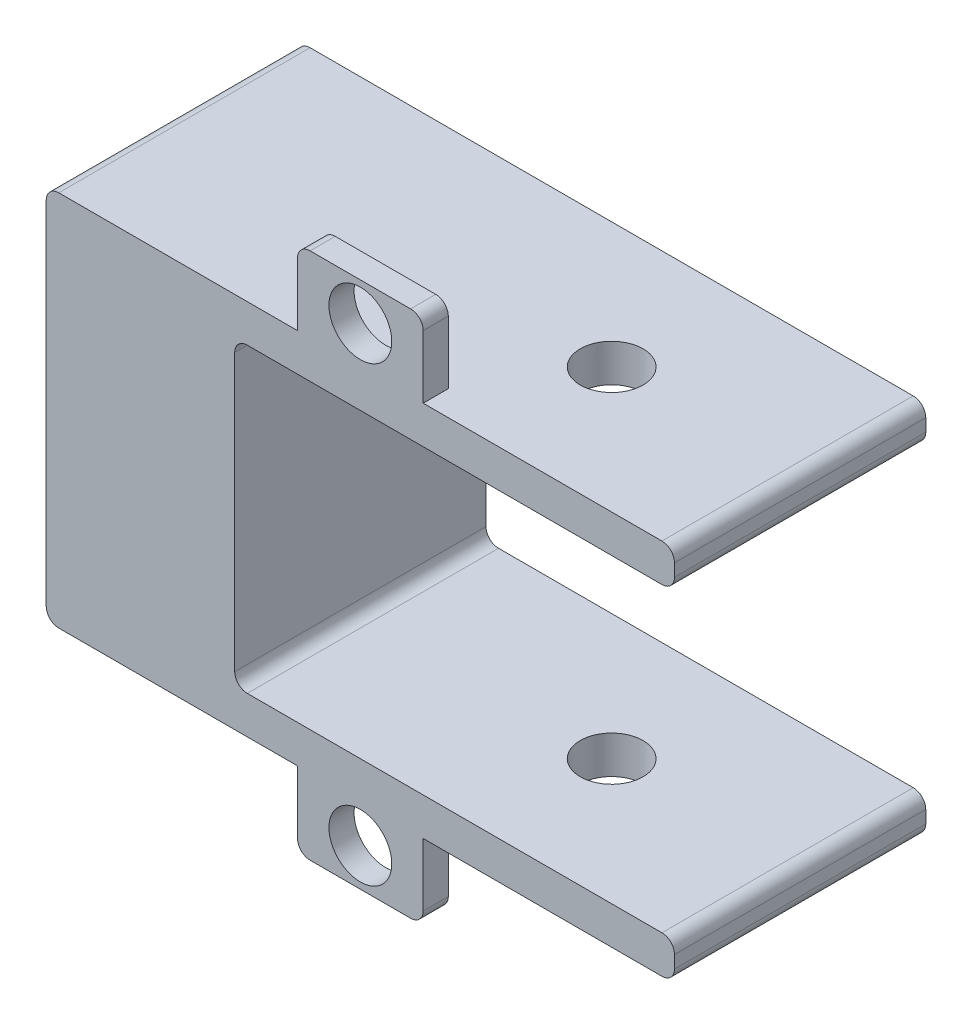
SolidWorks part; units mm, degrees
ref_plane "Front Plane" through (0, 0, 0) normal (0, 0, 1) x (1, 0, 0)
ref_plane "Top Plane" through (0, 0, 0) normal (0, 1, 0) x (1, 0, 0)
ref_plane "Right Plane" through (0, 0, 0) normal (1, 0, 0) x (0, 0, -1)
sketch "Sketch1" plane through (0, 0, 0) normal (0, 0, 1) x (1, 0, 0)
  line L1 (0, 0) -> (63.5, 0)
  line L2 (0, 0) -> (0, 38.1)
  line L3 (0, 38.1) -> (63.5, 38.1)
  line L4 (63.5, 0) -> (63.5, 38.1)
  dimension "D1" = 38.1
  dimension "D2" = 63.5
extrude "Boss-Extrude1" add sketch "Sketch1" along normal blind 25.4
sketch "Sketch3" plane through (0, 0, 0) normal (0, 0, -1) x (-1, 0, 0)
  line L0 (-63.5, 0) -> (-63.5, 38.1) construction
  line L1 (-63.5, 34.29) -> (-19.05, 34.29)
  line L2 (-63.5, 34.29) -> (-63.5, 3.81)
  line L3 (-63.5, 3.81) -> (-19.05, 3.81)
  line L4 (-19.05, 34.29) -> (-19.05, 3.81)
  line L9 (0, 0) -> (-63.5, 0) construction
  line L10 (-63.5, 38.1) -> (0, 38.1) construction
  dimension "D1" = 3.81
  dimension "D2" = 3.81
  dimension "D3" = 44.45
extrude "Cut-Extrude1" cut sketch "Sketch3" against normal blind 38.1
sketch "Sketch5" plane through (0, 0, 0) normal (0, -1, 0) x (1, 0, 0)
  line L0 (0, 0) -> (63.5, 0) construction
  circle A0 centre (44.45, 12.7) radius 3.175
  dimension "D1" = 6.35
  dimension "D2" = 12.7
  dimension "D3" = 19.05
extrude "Cut-Extrude2" cut sketch "Sketch5" against normal blind 76.2
fillet "Fillet3" radius 1.27 8 edges at (0, 38.1, 12.7) (0, 0, 12.7) (19.05, 3.81, 12.7) (19.05, 34.29, 12.7) (63.5, 3.81, 12.7) (63.5, 38.1, 12.7) (63.5, 34.29, 12.7) (63.5, 0, 12.7)
sketch "Sketch6" plane through (0, 38.1, 0) normal (0, 1, 0) x (1, 0, 0)
  line L5 (1.27, -25.4) -> (62.23, -25.4) construction
  line L6 (1.27, -22.86) -> (25.4, -22.86) construction
  line L7 (25.4, -25.4) -> (38.1, -25.4)
  line L8 (25.4, -25.4) -> (25.4, -22.86)
  line L9 (25.4, -22.86) -> (38.1, -22.86)
  line L10 (38.1, -25.4) -> (38.1, -22.86)
  line L11 (1.27, 0) -> (1.27, -25.4) construction
  line L12 (1.27, 0) -> (62.23, 0) construction
  dimension "D1" = 2.54
  dimension "D2" = 12.7
  dimension "D3" = 24.13
  dimension "D4" = 60.96
extrude "Boss-Extrude2" add sketch "Sketch6" along normal blind 7.62
sketch "Sketch7" plane through (0, 0, 0) normal (0, -1, 0) x (1, 0, 0)
  line L0 (62.23, 22.86) -> (38.1, 22.86) construction
  line L1 (62.23, 0) -> (62.23, 25.4) construction
  line L2 (1.27, 25.4) -> (62.23, 25.4) construction
  line L3 (38.1, 22.86) -> (25.4, 22.86)
  line L4 (38.1, 22.86) -> (38.1, 25.4)
  line L5 (38.1, 25.4) -> (25.4, 25.4)
  line L6 (25.4, 22.86) -> (25.4, 25.4)
  dimension "D1" = 24.13
  dimension "D2" = 12.7
  dimension "D3" = 2.54
extrude "Boss-Extrude3" add sketch "Sketch7" along normal blind 7.62 contours L3 L6 L5 L4
sketch "Sketch8" plane through (0, 0, 22.86) normal (0, 0, -1) x (-1, 0, 0)
  line L0 (-38.1, -3.81) -> (-25.4, -3.81) construction
  line L1 (-38.1, -7.62) -> (-38.1, 0) construction
  line L2 (-25.4, -7.62) -> (-25.4, 0) construction
  line L3 (-31.75, -7.62) -> (-31.75, 0) construction
  line L4 (-38.1, -7.62) -> (-25.4, -7.62) construction
  line L5 (-38.1, 0) -> (-25.4, 0) construction
  circle A0 centre (-31.75, -3.81) radius 3.175
  dimension "D1" = 6.35
extrude "Cut-Extrude3" cut sketch "Sketch8" against normal up to next
sketch "Sketch9" plane through (0, 0, 22.86) normal (0, 0, -1) x (-1, 0, 0)
  line L0 (-25.4, 41.91) -> (-38.1, 41.91) construction
  line L1 (-25.4, 45.72) -> (-25.4, 38.1) construction
  line L2 (-38.1, 45.72) -> (-38.1, 38.1) construction
  circle A0 centre (-31.75, 41.91) radius 3.175
  dimension "D1" = 6.35
extrude "Cut-Extrude4" cut sketch "Sketch9" against normal up to next
fillet "Fillet4" radius 1.27 4 edges at (25.4, -7.62, 24.13) (38.1, -7.62, 24.13) (25.4, 45.72, 24.13) (38.1, 45.72, 24.13)
